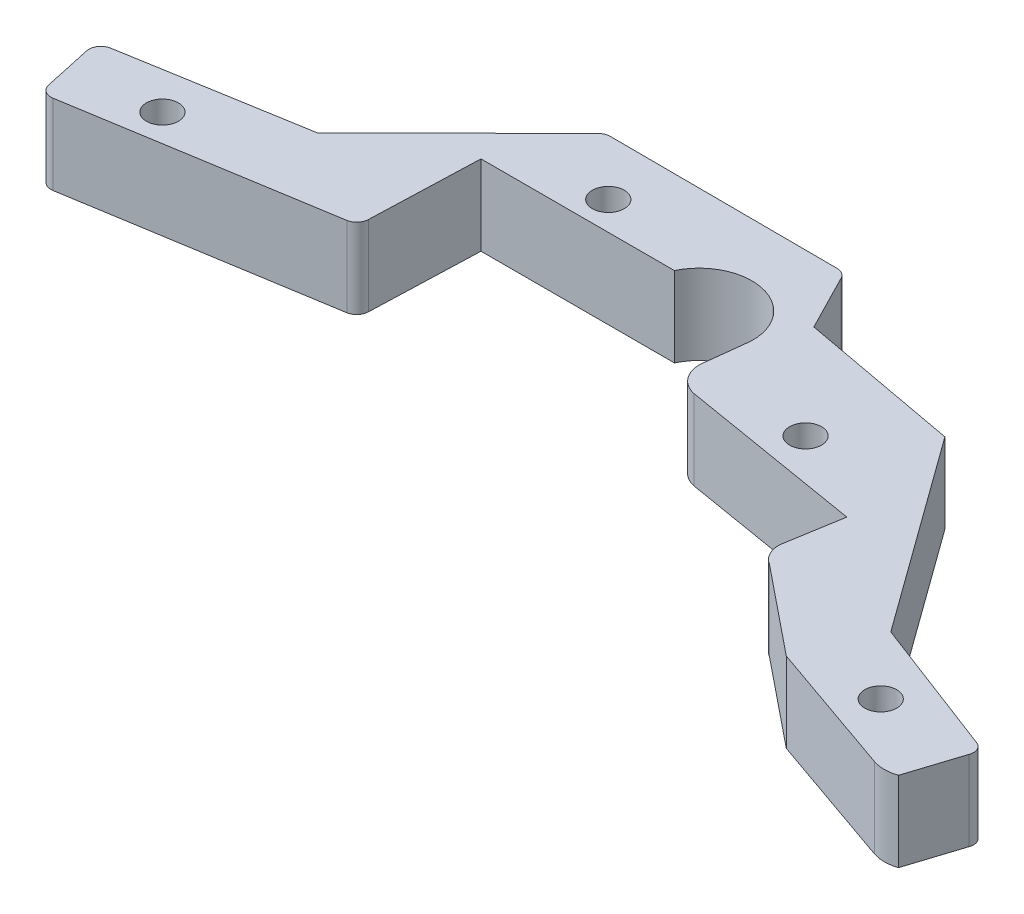
SolidWorks part; units mm, degrees
ref_plane "Front Plane" through (0, 0, 0) normal (0, 0, 1) x (1, 0, 0)
ref_plane "Top Plane" through (0, 0, 0) normal (0, 1, 0) x (1, 0, 0)
ref_plane "Right Plane" through (0, 0, 0) normal (1, 0, 0) x (0, 0, -1)
sketch "Sketch1" plane through (0, 0, 0) normal (0, 1, 0) x (1, 0, 0)
  line L0 (74.6071, 0.923) -> (714.6071, 0.923) construction
  line L1 (0, 0) -> (-0.9777, 4.493)
  line L10 (0, 0) -> (17.1013, 2.7798)
  line L18 (0, 0) -> (-0.9777, 4.493)
  line L19 (0, 0) -> (17.1013, 2.7798)
  line L20 (19.8733, 15.4617) -> (34.8631, 15.4012)
  line L21 (48.3276, -2.7351) -> (53.8072, -7.1654)
  line L22 (36.8586, 11.5057) -> (46.8999, 9.6547)
  line L23 (36.7079, 4.1579) -> (48.1788, 2.2457)
  line L24 (55.7698, -2.5962) -> (64.4495, -5.9078)
  line L25 (48.1788, 2.2457) -> (47.5889, -1.2929)
  line L26 (17.1013, 2.7798) -> (17.3597, 10.202)
  line L27 (53.8072, -7.1654) -> (62.2563, -10.1144)
  line L28 (34.8631, 15.4012) -> (36.8586, 11.5057)
  line L29 (17.3597, 10.202) -> (29.4471, 10.202)
  line L30 (10.8362, 6.4972) -> (19.8733, 15.4617)
  line L31 (35.6596, 8.7691) -> (35.3688, 6.2512)
  line L32 (-0.9777, 4.493) -> (10.8362, 6.4972)
  line L33 (46.8999, 9.6547) -> (55.7698, -2.5962)
  line L34 (64.8389, -6.7777) -> (63.7688, -10.1136)
  arc A5 (695.6006, -113.0097) -> (712.5006, -113.0008) centre (704.0379, -88.8357) ccw
  arc A11 (34.4478, 11.3762) -> (35.6596, 8.7691) centre (32.5148, 8.8925) cw
  arc A12 (47.5889, -1.2929) -> (48.3276, -2.7351) centre (49.1114, -1.4233) ccw
  arc A13 (62.2563, -10.1144) -> (63.7688, -10.1136) centre (63.0114, -7.9508) ccw
  circle A14 centre (23.5345, 11.9838) radius 1
  circle A15 centre (4.8701, 2.7798) radius 1
  arc A16 (64.4495, -5.9078) -> (64.8389, -6.7777) centre (64.2093, -6.5375) cw
  circle A17 centre (42.4959, 5.3498) radius 1
  arc A18 (35.3688, 6.2512) -> (36.7079, 4.1579) centre (37.085, 5.8741) ccw
  arc A19 (29.4471, 10.202) -> (34.4478, 11.3762) centre (32.421, 8.772) cw
  circle A20 centre (59.081, -6.5375) radius 1
  dimension "D1" = 2
  dimension "D2" = 2
  dimension "D3" = 2
  dimension "D4" = 2
extrude "Boss-Extrude1" add sketch "Sketch1" along normal blind 5 contours L29 A19 A11 L31 A18 L23 L25 A12 L21 L27 A13 L34 A16 L24 L33 L22 L28 L20 L30 L32 L1 L10 L26 A20 A14 A15 A17
fillet "Fillet1" radius 0.75 5 edges at (19.8733, 2.5, -15.4617) (17.1013, 2.5, -2.7798) (34.8631, 2.5, -15.4012) (-0.9777, 2.5, -4.493) (0, 2.5, 0)
